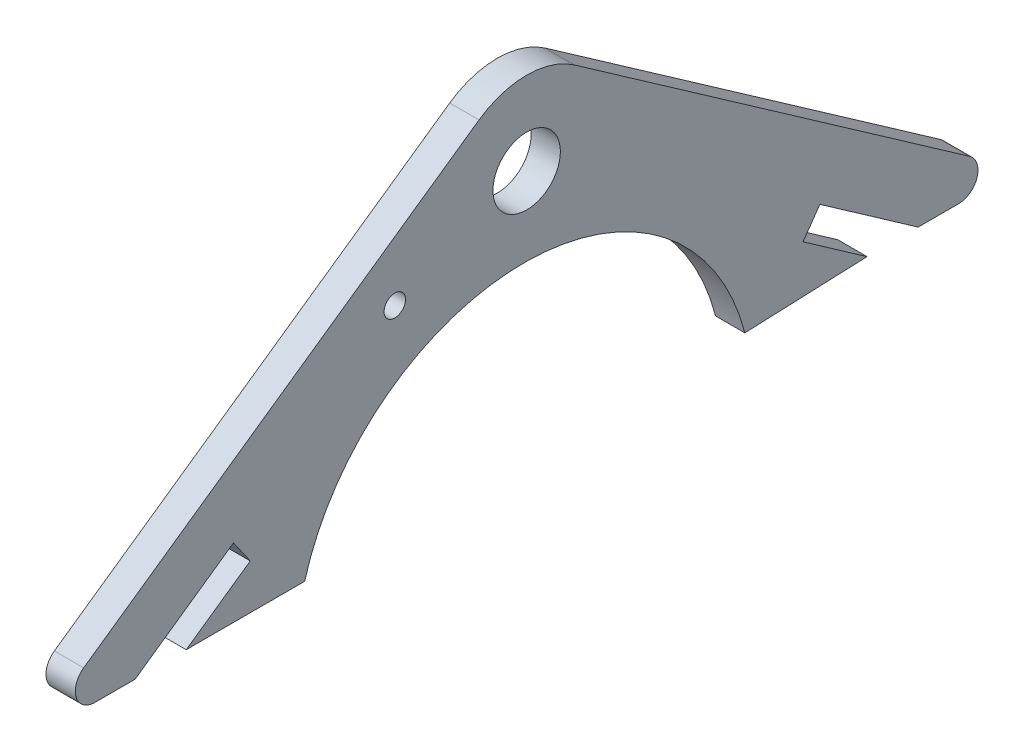
SolidWorks part; units mm, degrees
ref_plane "Front Plane" through (0, 0, 0) normal (0, 0, 1) x (1, 0, 0)
ref_plane "Top Plane" through (0, 0, 0) normal (0, 1, 0) x (1, 0, 0)
ref_plane "Right Plane" through (0, 0, 0) normal (1, 0, 0) x (0, 0, -1)
sketch "Sketch1" plane through (0, 0, 0) normal (1, 0, 0) x (0, 0, -1)
  line L0 (0, 0) -> (0, 9.7181) construction
  line L1 (0, 0) -> (-4.8754, 6.9628) construction
  line L2 (-4.8754, 6.9628) -> (-45.327, -21.3617)
  line L3 (0, 0) -> (0, -25) construction
  line L4 (-22.712, -25) -> (-34.832, -25)
  line L5 (-40.0623, -25) -> (-29.9995, -17.9539)
  line L6 (-40.0623, -25) -> (-44.1798, -25)
  line L7 (-29.9995, -17.9539) -> (-28.2788, -20.4114)
  line L8 (-34.832, -25) -> (-28.2788, -20.4114)
  line L9 (-38.4724, -16.5621) -> (-35.0309, -21.477) construction
  line L10 (0, 0) -> (-13.4918, -5.1743) construction
  line L11 (34.832, -25) -> (28.2788, -20.4114)
  line L12 (0, -25) -> (0, -8) construction
  line L13 (-16.3597, -1.0786) -> (-13.4918, -5.1743) construction
  line L15 (29.9995, -17.9539) -> (28.2788, -20.4114)
  line L16 (40.0623, -25) -> (44.1798, -25)
  line L17 (40.0623, -25) -> (29.9995, -17.9539)
  line L18 (22.3247, -25.5056) -> (34.832, -25)
  line L19 (4.8754, 6.9628) -> (45.327, -21.3617)
  line L20 (-50.523, -25) -> (-22.712, -25) construction
  arc A0 (4.8754, 6.9628) -> (-4.8754, 6.9628) centre (0, 0) ccw
  circle A1 centre (0, 0) radius 3.45
  arc A2 (45.327, -21.3617) -> (44.1798, -25) centre (44.1798, -23) cw
  arc A3 (-45.327, -21.3617) -> (-44.1798, -25) centre (-44.1798, -23) ccw
  circle A4 centre (-13.4918, -5.1743) radius 1.1
  arc A5 (-22.712, -25) -> (22.3247, -25.5056) centre (-0.2618, -31.3219) cw
  point P24 (50.523, -25)
  point P25 (50.523, -25)
  point P32 (0, -8)
  point P34 (0, -8)
  dimension "D1" = 8.5
  dimension "D9" = 6.9
  dimension "D10" = 2
  dimension "D11" = 23.3233
  dimension "D5" = 14.45
  dimension "D8" = 8
  dimension "D12" = 2.2
  dimension "D2" = 25
  dimension "D3" = 35
  dimension "D4" = 6
  dimension "D6" = 3
  dimension "D7" = 8
extrude "Boss-Extrude1" add sketch "Sketch1" along normal blind 3
